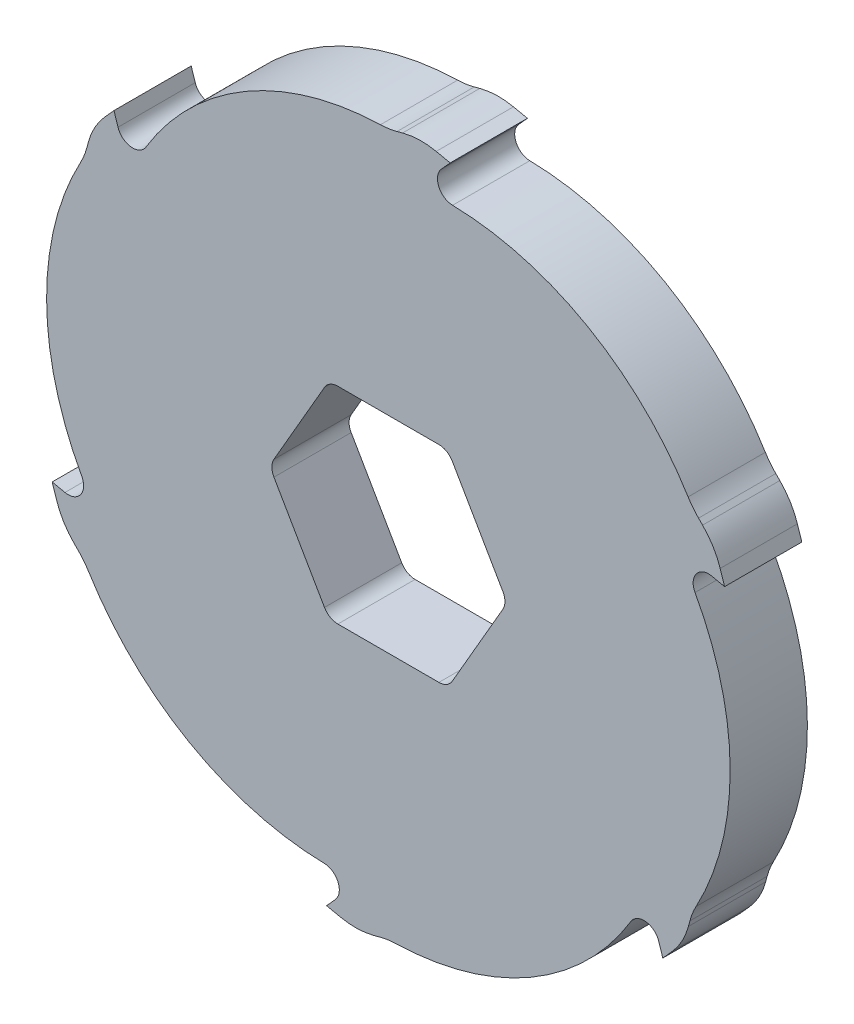
SolidWorks part; units mm, degrees
material "Tungsten"
ref_plane "Front Plane" through (0, 0, 0) normal (0, 0, 1) x (1, 0, 0)
ref_plane "Top Plane" through (0, 0, 0) normal (0, 1, 0) x (1, 0, 0)
ref_plane "Right Plane" through (0, 0, 0) normal (1, 0, 0) x (0, 0, -1)
sketch "Sketch1" plane through (0, 0, 0) normal (0, 0, 1) x (1, 0, 0)
  line L1 (23.094, 0) -> (11.547, 20)
  line L2 (11.547, 20) -> (-11.547, 20)
  line L3 (-11.547, 20) -> (-23.094, 0)
  line L4 (-23.094, 0) -> (-11.547, -20)
  line L5 (-11.547, -20) -> (11.547, -20)
  line L6 (11.547, -20) -> (23.094, 0)
  circle A0 centre (0, 0) radius 20 construction
  circle A1 centre (0, 0) radius 70
  dimension "D1" = 140
  dimension "D2" = 40
extrude "Boss-Extrude1" add sketch "Sketch1" along normal mid plane 15
fillet "Fillet1" radius 3 6 edges at (11.547, 20, 0) (-11.547, 20, 0) (-23.094, 0, 0) (11.547, -20, 0) (23.094, 0, 0) (-11.547, -20, 0)
sketch "Sketch3" plane through (0, 0, 0) normal (0, 0, 1) x (1, 0, 0)
  line L0 (0, 0) -> (0, 78.9123)
  line L1 (0, 68.1347) -> (6, 69.7424)
  line L2 (6, 69.7424) -> (12, 68.467)
  line L3 (12, 68.467) -> (5.5253, 61.2761)
  line L4 (59.0064, 34.0673) -> (63.3987, 29.675)
  line L5 (63.3987, 29.675) -> (65.2942, 23.8412)
  line L6 (65.2942, 23.8412) -> (55.8293, 25.853)
  line L7 (59.0064, -34.0673) -> (57.3987, -40.0673)
  line L8 (57.3987, -40.0673) -> (53.2942, -44.6258)
  line L9 (53.2942, -44.6258) -> (50.304, -35.4231)
  line L10 (0, -68.1347) -> (-6, -69.7424)
  line L11 (-6, -69.7424) -> (-12, -68.467)
  line L12 (-12, -68.467) -> (-5.5253, -61.2761)
  line L13 (-59.0064, -34.0673) -> (-63.3987, -29.675)
  line L14 (-63.3987, -29.675) -> (-65.2942, -23.8412)
  line L15 (-65.2942, -23.8412) -> (-55.8293, -25.853)
  line L16 (-59.0064, 34.0673) -> (-57.3987, 40.0673)
  line L17 (-57.3987, 40.0673) -> (-53.2942, 44.6258)
  line L18 (-53.2942, 44.6258) -> (-50.304, 35.4231)
  circle A0 centre (0, 0) radius 70 construction
  arc A1 (0, 68.1347) -> (-50.304, 35.4231) centre (0, 13.1) ccw
  arc A2 (59.0064, 34.0673) -> (5.5253, 61.2761) centre (11.3449, 6.55) ccw
  arc A3 (59.0064, -34.0673) -> (55.8293, 25.853) centre (11.3449, -6.55) ccw
  arc A4 (0, -68.1347) -> (50.304, -35.4231) centre (0, -13.1) ccw
  arc A5 (-59.0064, -34.0673) -> (-5.5253, -61.2761) centre (-11.3449, -6.55) ccw
  arc A6 (-59.0064, 34.0673) -> (-55.8293, -25.853) centre (-11.3449, 6.55) ccw
  circle A7 centre (0, 0) radius 70
  point P44 (0, 0)
  dimension "D7" = 6
  dimension "D8" = 140
  dimension "D1" = 78
  dimension "D2" = 6
  dimension "D3" = 12
  dimension "D4" = 60
  dimension "D5" = 105
  dimension "D6" = 13.1
extrude "Cut-Extrude2" cut sketch "Sketch3" against normal through all both and the other way through all contours L4 A7 L2 L3 A2 | L0 A7 L17 L18 A1 | L7 A7 L5 L6 A3 | L16 A7 L14 L15 A6 | L13 A7 L11 L12 A5 | L10 A7 L8 L9 A4
sketch "Sketch4" plane through (0, 0, 7.5) normal (0, 0, 1) x (1, 0, 0)
  line L0 (0, 68.1347) -> (6, 69.7424)
  line L1 (6, 69.7424) -> (0, 70)
  line L2 (0, 70) -> (0, 68.1347)
  arc A0 (6, 69.7424) -> (0, 70) centre (0, 0) ccw construction
extrude "Cut-Extrude3" cut sketch "Sketch4" against normal through all both
fillet "Fillet2" radius 14 12 edges at (63.3987, 29.675, 0) (59.0064, 34.0673, 0) (57.3987, -40.0673, 0) (59.0064, -34.0673, 0) (0, -68.1347, 0) (-6, -69.7424, 0) (-63.3987, -29.675, 0) (-59.0064, -34.0673, 0) (-57.3987, 40.0673, 0) (-59.0064, 34.0673, 0) (6, 69.7424, 0) (0, 68.1347, 0)
fillet "Fillet3" radius 3 6 edges at (-55.8293, -25.853, 0) (-5.5253, -61.2761, 0) (50.304, -35.4231, 0) (55.8293, 25.853, 0) (5.5253, 61.2761, 0) (-50.304, 35.4231, 0)
